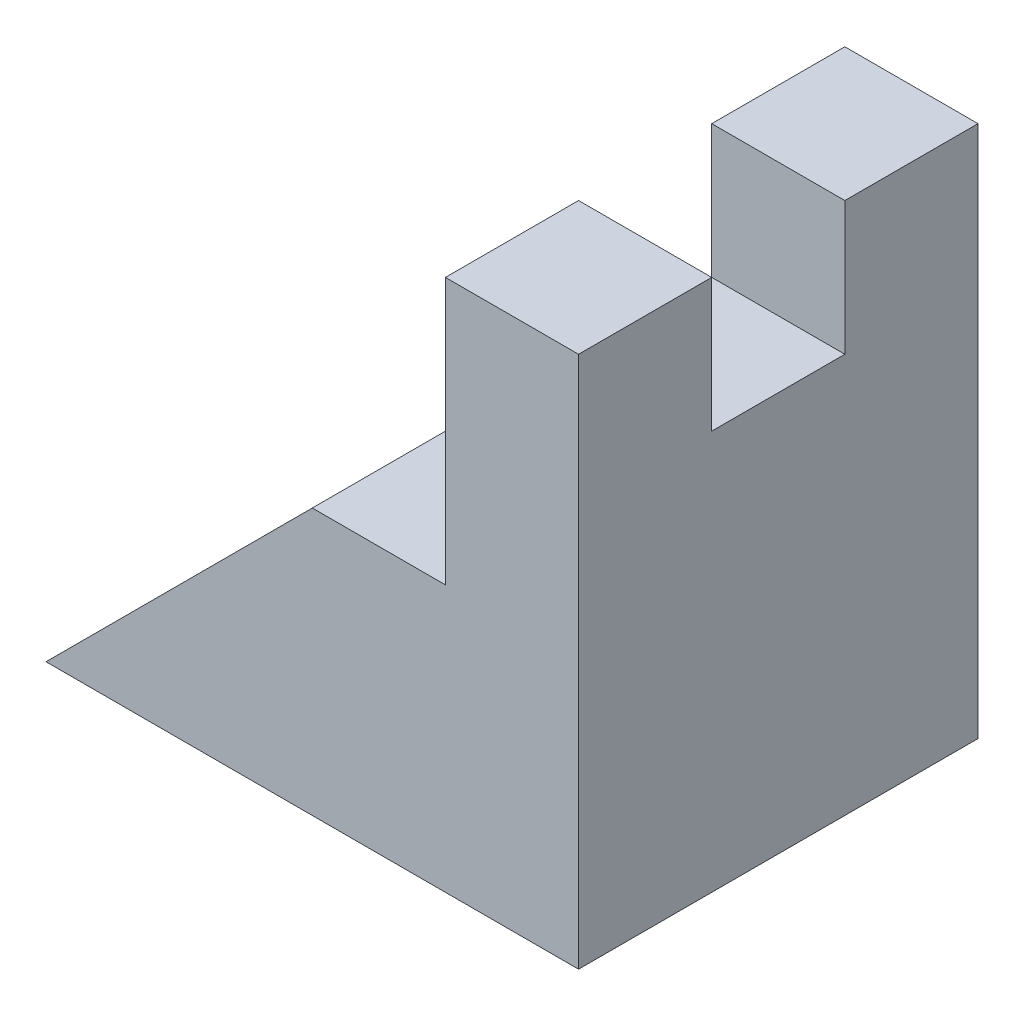
SolidWorks part; units mm, degrees
material "AISI 1020"
ref_plane "Plano frontal" through (0, 0, 0) normal (0, 0, 1) x (1, 0, 0)
ref_plane "Plano superior" through (0, 0, 0) normal (0, 1, 0) x (1, 0, 0)
ref_plane "Plano direito" through (0, 0, 0) normal (1, 0, 0) x (0, 0, -1)
sketch "Esboço1" plane through (0, 0, 0) normal (0, 0, 1) x (1, 0, 0)
  line L0 (0, 0) -> (20, 20)
  line L1 (20, 20) -> (30, 20)
  line L2 (30, 20) -> (30, 40)
  line L3 (30, 40) -> (40, 40)
  line L4 (40, 40) -> (40, 0)
  line L5 (40, 0) -> (0, 0)
  dimension "D1" = 40
  dimension "D2" = 40
  dimension "D3" = 10
  dimension "D4" = 45
  dimension "D5" = 20
extrude "Ressalto-extrusão1" add sketch "Esboço1" along normal mid plane 30
sketch "Esboço2" plane through (40, 0, 0) normal (1, 0, 0) x (0, 0, -1)
  line L0 (-5, 40) -> (-5, 30)
  line L1 (-15, 40) -> (15, 40) construction
  line L2 (-5, 30) -> (5, 30)
  line L3 (5, 30) -> (5, 40)
  line L4 (5, 40) -> (-5, 40)
  line L5 (0, 30) -> (0, 0) construction
  line L6 (-15, 0) -> (15, 0) construction
  dimension "D1" = 10
extrude "Corte-extrusão1" cut sketch "Esboço2" against normal through all
